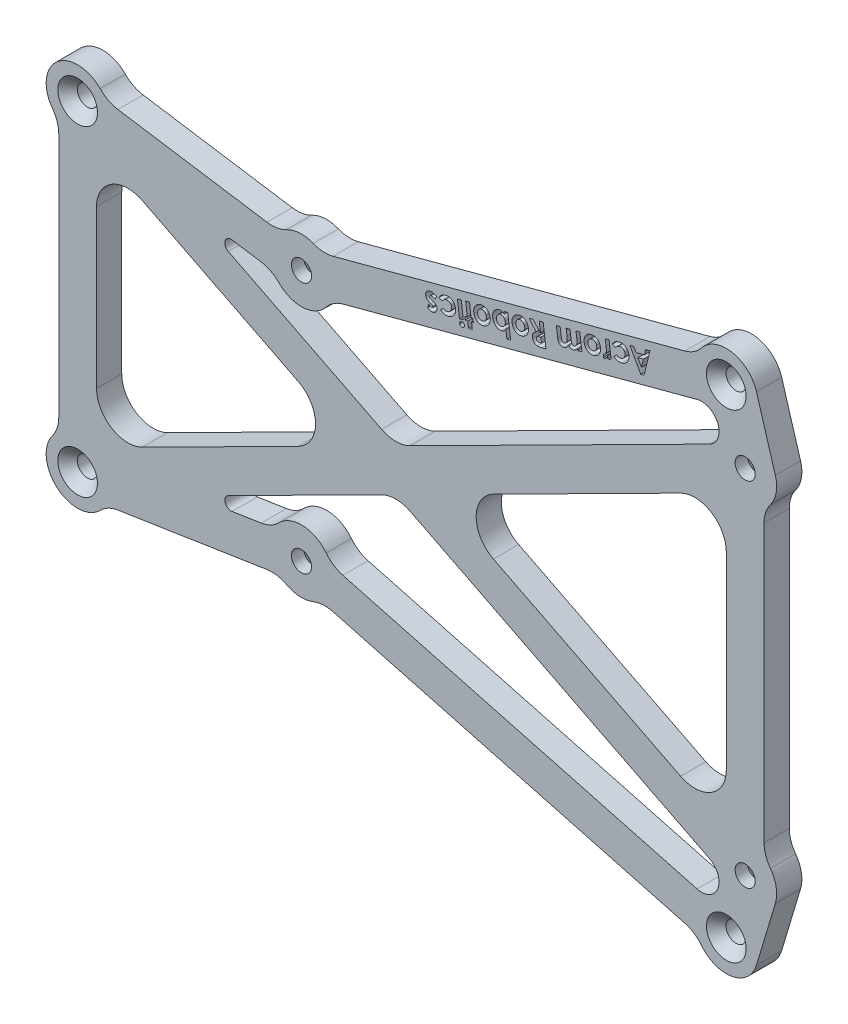
SolidWorks part; units mm, degrees
material "ABS"
ref_plane "Plan de face" through (0, 0, 0) normal (0, 0, 1) x (1, 0, 0)
ref_plane "Plan de dessus" through (0, 0, 0) normal (0, 1, 0) x (1, 0, 0)
ref_plane "Plan de droite" through (0, 0, 0) normal (1, 0, 0) x (0, 0, -1)
sketch "Esquisse1" plane through (0, 0, 0) normal (0, 0, 1) x (1, 0, 0)
  line L10 (-114.009, 0) -> (157.7082, 0) construction
  line L21 (-71.6118, 27.5471) -> (-47.9306, 23.8823)
  line L22 (-37.4362, 24.4454) -> (18.4294, 39.3518)
  line L34 (31, 22) -> (31, -22)
  line L41 (28, 28) -> (28, -28) construction
  line L42 (-78, 25.5) -> (-42.46, 20) construction
  line L43 (-42.46, -20) -> (-42.46, 20) construction
  line L44 (-42.46, 20) -> (25, 38) construction
  line L45 (25, 38) -> (28, 28) construction
  line L46 (-78, 25.5) -> (-78, -25.5) construction
  line L47 (-78, -25.5) -> (-42.46, -20) construction
  line L48 (-42.46, -20) -> (25, -38) construction
  line L49 (25, -38) -> (28, -28) construction
  line L51 (-37.4362, -24.4454) -> (18.4294, -39.3518)
  line L52 (-71.6118, -27.5471) -> (-47.9306, -23.8823)
  line L53 (-81, 19.5) -> (-81, -19.5)
  line L55 (-35.8894, 18.6482) -> (20.3618, 33.6575)
  line L56 (23.2759, 33.3067) -> (23.9771, 30.9693) construction
  line L57 (25, 15.0011) -> (25, -15.0011)
  line L58 (23.2759, -33.3067) -> (23.9771, -30.9693) construction
  line L59 (-35.8894, -18.6482) -> (20.3618, -33.6575)
  line L61 (-75, 12.5011) -> (-75, -12.5011)
  line L62 (-78, 25.5) -> (28, -28) construction
  line L63 (-81, 29) -> (-81, -29) construction
  line L64 (-81, 29) -> (-42.6243, 23.0611) construction
  line L65 (-75, 22) -> (-42.2957, 16.9389) construction
  line L66 (-75, 22) -> (-75, -22) construction
  line L67 (-75, -22) -> (-42.2957, -16.9389) construction
  line L68 (-81, -29) -> (-42.6243, -23.0611) construction
  line L69 (25, 27.5597) -> (25, -27.5597) construction
  line L70 (-42.2957, -16.9389) -> (22.9625, -34.3514) construction
  line L71 (-42.6243, -23.0611) -> (27.0375, -41.6486) construction
  line L72 (22.9625, -34.3514) -> (25, -27.5597) construction
  line L73 (27.0375, -41.6486) -> (31, -28.4403) construction
  line L74 (31, 28.4403) -> (31, -28.4403) construction
  line L75 (22.9625, 34.3514) -> (25, 27.5597) construction
  line L76 (27.0375, 41.6486) -> (31, 28.4403) construction
  line L77 (-42.2957, 16.9389) -> (22.9625, 34.3514) construction
  line L78 (-42.6243, 23.0611) -> (27.0375, 41.6486) construction
  line L79 (-78, -25.5) -> (28, 28) construction
  line L80 (-67.7471, 16.9647) -> (-42.9787, 4.4637)
  line L81 (-54.0816, -16.7884) -> (-29.7295, -4.4975)
  line L82 (-54.0816, 16.7884) -> (-29.7295, 4.4975)
  line L83 (-67.7471, -16.9647) -> (-42.9787, -4.4637)
  line L84 (-53.4781, 18.6694) -> (-48.8482, 17.9529)
  line L85 (-76.6483, 28.1782) -> (29.3517, -25.3218) construction
  line L86 (-79.3517, 22.8218) -> (26.6483, -30.6782) construction
  line L87 (-53.4781, -18.6694) -> (-48.8482, -17.9529)
  line L88 (-79.3517, -22.8218) -> (26.6483, 30.6782) construction
  line L89 (-76.6483, -28.1782) -> (29.3517, 25.3218) construction
  line L90 (-25.2237, -4.4975) -> (22.328, -28.4977)
  line L91 (-11.9746, -4.4637) -> (17.7471, -19.4647)
  line L92 (-25.2237, 4.4975) -> (22.328, 28.4977)
  line L93 (-11.9746, 4.4637) -> (17.7471, 19.4647)
  line L94 (32.7891, 29.4367) -> (29.7891, 39.4367)
  line L95 (32.7891, -29.4367) -> (29.7891, -39.4367)
  arc A4 (32, 25) -> (32.7891, 29.4367) centre (28, 28) ccw
  arc A5 (32.7891, -29.4367) -> (32, -25) centre (28, -28) ccw
  arc A6 (-44.813, -24.4117) -> (-40.5926, -24.6382) centre (-42.46, -20) ccw
  arc A7 (-46.0364, 16.5059) -> (-38.5302, 16.9086) centre (-42.46, 20) ccw
  arc A12 (-74.4236, 28.9941) -> (-82, 22.5) centre (-78, 25.5) ccw
  arc A13 (-82, -22.5) -> (-74.4236, -28.9941) centre (-78, -25.5) ccw
  arc A14 (-38.5302, -16.9086) -> (-46.0364, -16.5059) centre (-42.46, -20) ccw
  arc A15 (21.0702, -41.0914) -> (29.7891, -39.4367) centre (25, -38) ccw
  arc A18 (29.7891, 39.4367) -> (21.0702, 41.0914) centre (25, 38) ccw
  arc A19 (-40.5926, 24.6382) -> (-44.813, 24.4117) centre (-42.46, 20) ccw
  arc A20 (-81, 19.5) -> (-82, 22.5) centre (-86, 19.5) ccw
  arc A21 (-71.6118, 27.5471) -> (-74.4236, 28.9941) centre (-70.8471, 32.4883) cw
  arc A22 (-47.9306, 23.8823) -> (-44.813, 24.4117) centre (-47.1659, 28.8235) ccw
  arc A23 (-37.4362, 24.4454) -> (-40.5926, 24.6382) centre (-38.7253, 29.2764) cw
  arc A24 (18.4294, 39.3518) -> (21.0702, 41.0914) centre (17.1404, 44.1827) ccw
  arc A26 (32, 25) -> (31, 22) centre (36, 22) ccw
  arc A27 (17.7471, 19.4647) -> (25, 15.0011) centre (20, 15.0011) cw
  arc A28 (17.7471, -19.4647) -> (25, -15.0011) centre (20, -15.0011) ccw
  arc A29 (31, -22) -> (32, -25) centre (36, -22) ccw
  arc A30 (21.0702, -41.0914) -> (18.4294, -39.3518) centre (17.1404, -44.1827) ccw
  arc A31 (-46.0364, -16.5059) -> (-48.8482, -17.9529) centre (-49.6129, -13.0117) cw
  arc A32 (-35.8894, -18.6482) -> (-38.5302, -16.9086) centre (-34.6004, -13.8173) cw
  arc A33 (-37.4362, -24.4454) -> (-40.5926, -24.6382) centre (-38.7253, -29.2764) ccw
  arc A34 (-44.813, -24.4117) -> (-47.9306, -23.8823) centre (-47.1659, -28.8235) ccw
  arc A35 (-71.6118, -27.5471) -> (-74.4236, -28.9941) centre (-70.8471, -32.4883) ccw
  arc A36 (-81, -19.5) -> (-82, -22.5) centre (-86, -19.5) cw
  arc A37 (-48.8482, 17.9529) -> (-46.0364, 16.5059) centre (-49.6129, 13.0117) cw
  arc A38 (-35.8894, 18.6482) -> (-38.5302, 16.9086) centre (-34.6004, 13.8173) ccw
  arc A39 (-11.9746, -4.4637) -> (-11.9746, 4.4637) centre (-9.7217, 0) cw
  arc A40 (-29.7295, 4.4975) -> (-25.2237, 4.4975) centre (-27.4766, 8.9612) ccw
  arc A41 (-25.2237, -4.4975) -> (-29.7295, -4.4975) centre (-27.4766, -8.9612) ccw
  arc A42 (-42.9787, 4.4637) -> (-42.9787, -4.4637) centre (-45.2316, 0) cw
  arc A43 (-75, -12.5011) -> (-67.7471, -16.9647) centre (-70, -12.5011) ccw
  arc A44 (-67.7471, 16.9647) -> (-75, 12.5011) centre (-70, 12.5011) ccw
  arc A45 (-54.0816, -16.7884) -> (-53.4781, -18.6694) centre (-53.631, -17.6812) ccw
  arc A46 (-54.0816, 16.7884) -> (-53.4781, 18.6694) centre (-53.631, 17.6812) cw
  arc A47 (22.328, 28.4977) -> (20.3618, 33.6575) centre (21.0774, 30.9756) ccw
  arc A48 (22.328, -28.4977) -> (20.3618, -33.6575) centre (21.0774, -30.9756) cw
  point P0 (0, 0)
  point P7 (0, 0)
  point P17 (-43.5, -51)
  point P22 (63, 0)
  point P27 (28, 28)
  point P29 (0, 0)
  point P30 (28, -28)
  point P31 (-42.46, 20)
  point P32 (-42.46, -20)
  point P36 (28, 0)
  point P38 (-42.46, 0)
  point P52 (0, 0)
  point P108 (-39.3686, 23.9298)
  point P127 (-37.8218, -18.1326)
  point P144 (-27.4766, 3.3605)
  dimension "D4" = 5
  dimension "D10" = 5
  dimension "D11" = 1
  dimension "D1" = 70.46
  dimension "D2" = 40
  dimension "D3" = 56
  dimension "D5" = 28
  dimension "D6" = 3
  dimension "D7" = 3
  dimension "D8" = 3
  dimension "D9" = 3
extrude "Boss.-Extru.1" add sketch "Esquisse1" along normal blind 4
hole_wizard "Fraisage pour vis à tête fraisée M32" positions "Esquisse2" profile "Esquisse3" countersink size "M3" standard "ISO" end condition up to next
sketch "Esquisse2" plane through (0, 0, 4) normal (0, 0, 1) x (1, 0, 0)
  point P0 (-78, 25.5)
  point P3 (-78, -25.5)
  point P6 (25, 38)
  point P9 (25, -38)
sketch "Esquisse3" plane through (-78, 25.5, 4) normal (1, 0, 0) x (0, -1, 0)
  line L0 (0, 0) -> (0, 4)
  line L1 (0, 4) -> (1.6, 4)
  line L2 (1.6, 4) -> (1.6, 1.55)
  line L3 (1.6, 1.55) -> (3.15, 0)
  line L5 (3.15, 0) -> (0, 0)
  line L6 (-1.6, 1.55) -> (-3.15, 0) construction
  line L11 (0, -6.35) -> (0, 107.95) construction
  dimension "Diamètre du perçage jusqu'au prochain" = 3.2
  dimension "Profondeur du perçage jusqu'au prochain" = 4
  dimension "Diamètre du fraisage entrant" = 6.3
  dimension "Angle du fraisage entrant" = 90
hole_wizard "Fraisage pour vis à tête fraisée M31" positions "Esquisse4" profile "Esquisse5" countersink size "M3" standard "ISO" end condition up to next
sketch "Esquisse4" plane through (0, 0, 0) normal (0, 0, -1) x (-1, 0, 0)
  point P0 (42.46, 20)
  point P3 (42.46, -20)
  point P6 (-28, 28)
  point P9 (-28, -28)
sketch "Esquisse5" plane through (-42.46, 20, 0) normal (1, 0, 0) x (0, 1, 0)
  line L0 (0, 0) -> (0, 4)
  line L1 (0, 4) -> (1.6, 4)
  line L2 (1.6, 4) -> (1.6, 2.05)
  line L3 (1.6, 2.05) -> (3.65, 0)
  line L5 (3.65, 0) -> (0, 0)
  line L6 (-1.6, 2.05) -> (-3.65, 0) construction
  line L11 (0, -6.35) -> (0, 107.95) construction
  dimension "Diamètre du perçage jusqu'au prochain" = 3.2
  dimension "Profondeur du perçage jusqu'au prochain" = 4
  dimension "Diamètre du fraisage entrant" = 7.3
  dimension "Angle du fraisage entrant" = 90
sketch "Esquisse6" plane through (0, 0, 4) normal (0, 0, 1) x (1, 0, 0)
  line L0 (12.811, 36.5865) -> (-32.5253, 24.4896) construction
  line L2 (18.4294, 39.3518) -> (-37.4362, 24.4454) construction
  text T0 "<b><i>Acrom Robotics</i></b>"
extrude "Enlèv. mat.-Extru.2" cut sketch "Esquisse6" against normal blind 2
